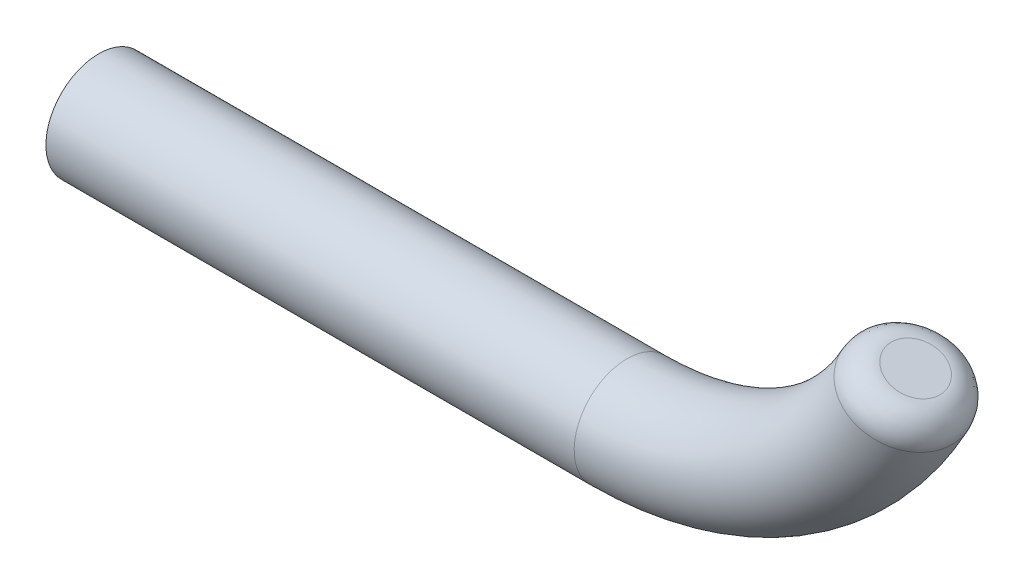
SolidWorks part; units mm, degrees
ref_plane "Front Plane" through (0, 0, 0) normal (0, 0, 1) x (1, 0, 0)
ref_plane "Top Plane" through (0, 0, 0) normal (0, 1, 0) x (1, 0, 0)
ref_plane "Right Plane" through (0, 0, 0) normal (1, 0, 0) x (0, 0, -1)
sketch "Sketch1" plane through (0, 0, 0) normal (0, 0, 1) x (1, 0, 0)
  line L2 (0, -5) -> (50, -5)
  arc A1 (50, -5) -> (77.4143, 12.8158) centre (50, 25) ccw
  dimension "D2" = 30
sketch "Sketch2" plane through (0, 0, 0) normal (1, 0, 0) x (0, 0, -1)
  circle A0 centre (0, -5) radius 5
sweep "Sweep1" add profiles "Sketch2" path "Sketch1"
fillet "Fillet1" radius 2.5 1 edges at (77.4143, 12.8158, -5)
